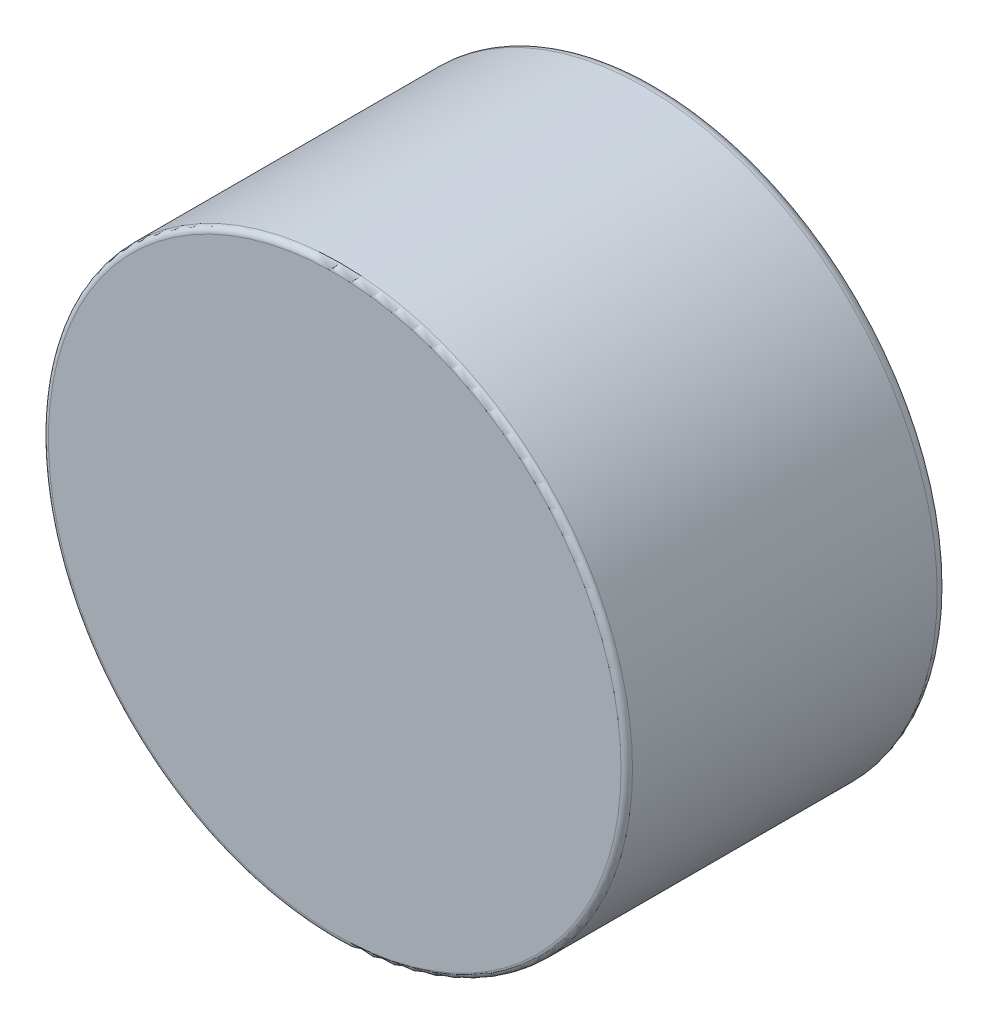
SolidWorks part; units mm, degrees
ref_plane "Front Plane" through (0, 0, 0) normal (0, 0, 1) x (1, 0, 0)
ref_plane "Top Plane" through (0, 0, 0) normal (0, 1, 0) x (1, 0, 0)
ref_plane "Right Plane" through (0, 0, 0) normal (1, 0, 0) x (0, 0, -1)
sketch "Sketch1" plane through (0, 0, 0) normal (0, 0, 1) x (1, 0, 0)
  circle A0 centre (0, 0) radius 25.4
  circle A1 centre (0, 0) radius 21.4
  dimension "D1" = 50.8
  dimension "D2" = 42.8
extrude "Boss-Extrude1" add sketch "Sketch1" along normal blind 28
sketch "Sketch2" plane through (0, 0, 28) normal (0, 0, 1) x (1, 0, 0)
  circle A0 centre (0, 0) radius 21.4
extrude "Boss-Extrude3" add sketch "Sketch2" against normal blind 5
fillet "Fillet3" radius 2 1 edges at (21.4, 0, 0)
fillet "Fillet4" radius 1 1 edges at (25.4, 0, 0)
fillet "Fillet5" radius 0.5 1 edges at (25.4, 0, 28)
